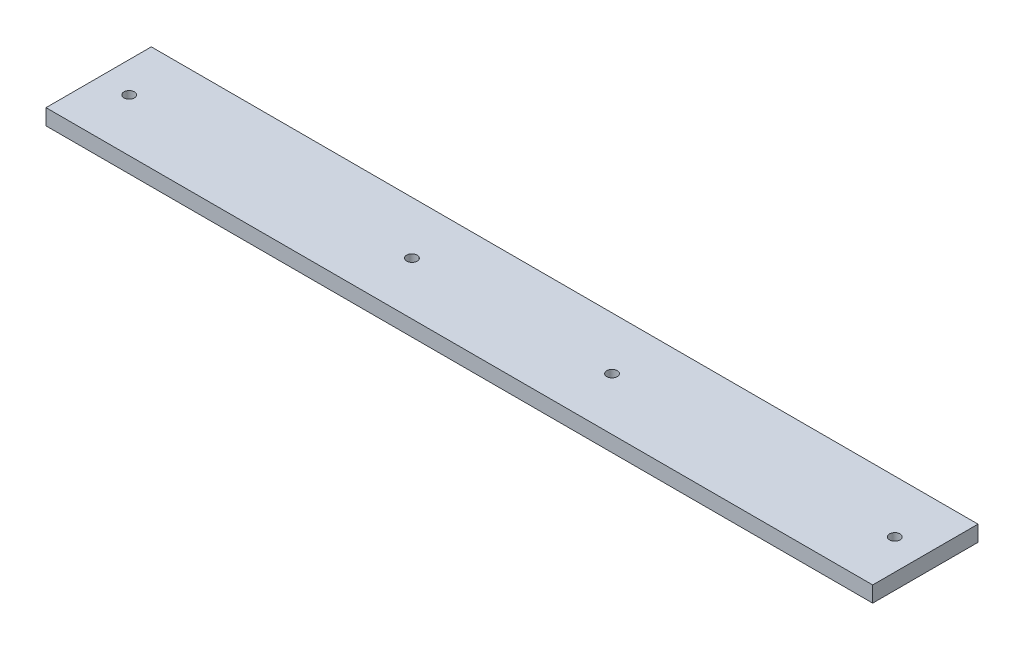
SolidWorks part; units mm, degrees
ref_plane "Alzado" through (0, 0, 0) normal (0, 0, 1) x (1, 0, 0)
ref_plane "Planta" through (0, 0, 0) normal (0, 1, 0) x (1, 0, 0)
ref_plane "Vista lateral" through (0, 0, 0) normal (1, 0, 0) x (0, 0, -1)
sketch "Croquis1" plane through (0, 0, 0) normal (0, 1, 0) x (1, 0, 0)
  line L1 (-38.5634, 7.6669) -> (746.4366, 7.6669)
  line L2 (-38.5634, 7.6669) -> (-38.5634, -92.3331)
  line L3 (-38.5634, -92.3331) -> (746.4366, -92.3331)
  line L4 (746.4366, 7.6669) -> (746.4366, -92.3331)
  dimension "D1" = 785
  dimension "10.2" = 100
extrude "Saliente-Extruir1" add sketch "Croquis1" against normal blind 15 contours L1 L4 L3 L2
sketch "Croquis5" plane through (0, 0, 0) normal (0, 1, 0) x (1, 0, 0)
  line L0 (-38.5634, -92.3331) -> (746.4366, -92.3331) construction
  line L1 (-38.5634, 7.6669) -> (-38.5634, -92.3331) construction
  circle A0 centre (258.9366, -42.3331) radius 5
  circle A1 centre (448.9366, -42.3331) radius 5
  dimension "D1" = 10
  dimension "D4" = 10
  dimension "D2" = 50
  dimension "D3" = 297.5
  dimension "D5" = 190
  dimension "D6" = 50
extrude "Cortar-Extruir4" cut sketch "Croquis5" against normal through all
sketch "Croquis6" plane through (0, 0, 0) normal (0, 1, 0) x (1, 0, 0)
  line L0 (746.4366, 7.6669) -> (746.4366, -92.3331) construction
  line L3 (-38.5634, -92.3331) -> (746.4366, -92.3331) construction
  line L4 (-38.5634, 7.6669) -> (-38.5634, -92.3331) construction
  line L5 (-38.5634, 7.6669) -> (746.4366, 7.6669) construction
  circle A0 centre (-9.5634, -42.3331) radius 5
  circle A1 centre (717.4366, -42.3331) radius 5
  dimension "D1" = 10
  dimension "D4" = 50
  dimension "D5" = 29
  dimension "D3" = 29
  dimension "D2" = 10
  dimension "D6" = 50
extrude "Cortar-Extruir5" cut sketch "Croquis6" against normal through all
